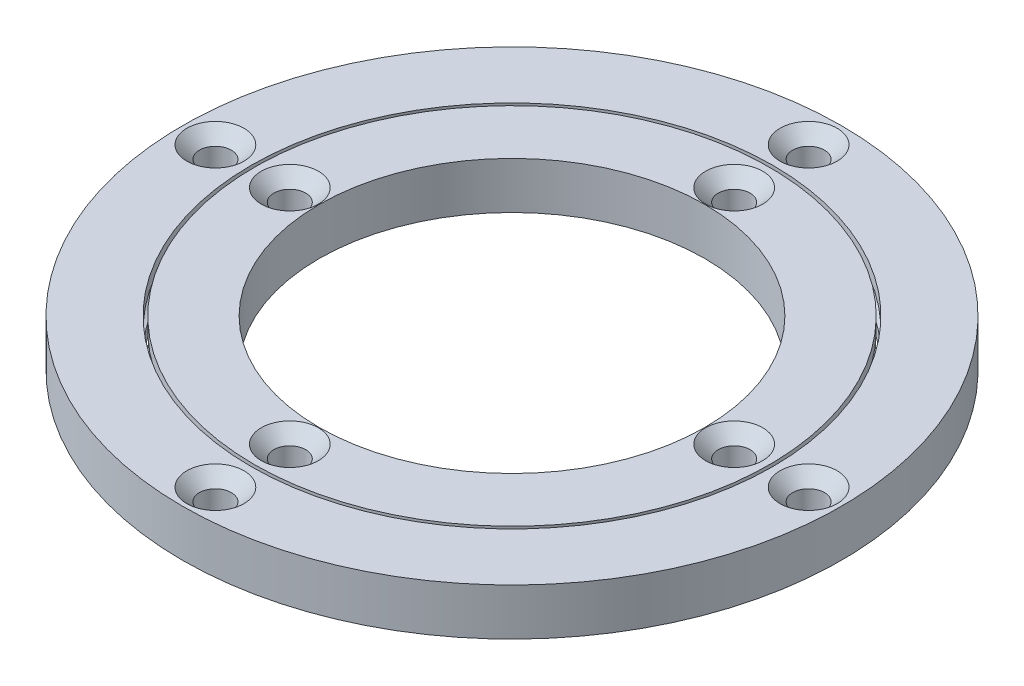
SolidWorks part; units mm, degrees
ref_plane "Front" through (0, 0, 0) normal (0, 0, 1) x (1, 0, 0)
ref_plane "Top" through (0, 0, 0) normal (0, 1, 0) x (1, 0, 0)
ref_plane "Right" through (0, 0, 0) normal (1, 0, 0) x (0, 0, -1)
sketch "Sketch1" plane through (0, 0, 0) normal (0, 1, 0) x (1, 0, 0)
  circle A0 centre (0, 0) radius 60
  circle A1 centre (0, 0) radius 47.5
  dimension "D1" = 120
  dimension "D2" = 95
extrude "Boss-Extrude1" add sketch "Sketch1" along normal blind 8.53
sketch "Sketch2" plane through (0, 0, 0) normal (0, 1, 0) x (1, 0, 0)
  circle A0 centre (0, 0) radius 46.89
  circle A1 centre (0, 0) radius 35.135
  dimension "D1" = 93.78
  dimension "D2" = 70.27
extrude "Boss-Extrude2" add sketch "Sketch2" along normal up to surface (8.53 mm away) separate body up to face at (0, 8.53, 60)
ref_plane "Plane1" through (0, 4.265, 0) normal (0, 1, 0) x (1, 0, 0)
sketch "Sketch3" plane through (0, 4.265, 0) normal (0, 1, 0) x (1, 0, 0)
  line L0 (0, 46.89) -> (0, 47.195) construction
  line L1 (0, 47.195) -> (0, 47.5) construction
  circle A0 centre (0, 0) radius 47.195
  circle A1 centre (0, 0) radius 46.89 construction
  circle A2 centre (0, 0) radius 47.5 construction
sweep "Cut-Sweep1" cut path "Sketch3" circular profile diameter 4 parameters "D3"=4
sketch "Sketch31" plane through (0, 8.53, 0) normal (0, 1, 0) x (1, 0, 0)
  line L0 (0, 0) -> (0, 40.45) construction
  line L1 (0, 40.45) -> (0, 54) construction
  circle A0 centre (0, 40.45) radius 2.5
  circle A1 centre (0, 54) radius 2.5
  circle A5 centre (40.45, 0) radius 2.5
  circle A6 centre (54, 0) radius 2.5
  circle A7 centre (0, -40.45) radius 2.5
  circle A8 centre (0, -54) radius 2.5
  circle A9 centre (-40.45, 0) radius 2.5
  circle A10 centre (-54, 0) radius 2.5
  point P6 (68.2002, 9.2524)
  point P7 (0, 0)
  point P21 (0, 0)
  dimension "D1" = 5
  dimension "D2" = 42.95
  dimension "D3" = 51.5
  dimension "D4" = 4
hole_wizard "CSK for M5 Flat Head Machine Screw1" positions "Sketch32" profile "Sketch33" countersink size "M5" standard "ANSI Metric" end condition through all
sketch "Sketch32" plane through (0, 8.53, 0) normal (0, 1, 0) x (1, 0, 0)
  point P0 (0, 54)
  point P3 (0, 40.45)
  point P6 (40.45, 0)
  point P9 (54, 0)
  point P12 (-40.45, 0)
  point P15 (-54, 0)
  point P18 (0, -40.45)
  point P21 (0, -54)
sketch "Sketch33" plane through (0, 8.53, -54) normal (1, 0, 0) x (0, 0, 1)
  line L0 (0, 0) -> (0, 8.53)
  line L1 (0, 8.53) -> (2.9, 8.53)
  line L2 (2.9, 8.53) -> (2.9, 2.3)
  line L3 (2.9, 2.3) -> (5.2, 0)
  line L5 (5.2, 0) -> (0, 0)
  line L6 (-2.9, 2.3) -> (-5.2, 0) construction
  line L11 (0, -6.35) -> (0, 107.95) construction
  dimension "Thru Hole Dia." = 5.8
  dimension "Thru Hole Depth" = 8.53
  dimension "Near C'Sink Dia." = 10.4
  dimension "Near C'Sink Angle" = 90
